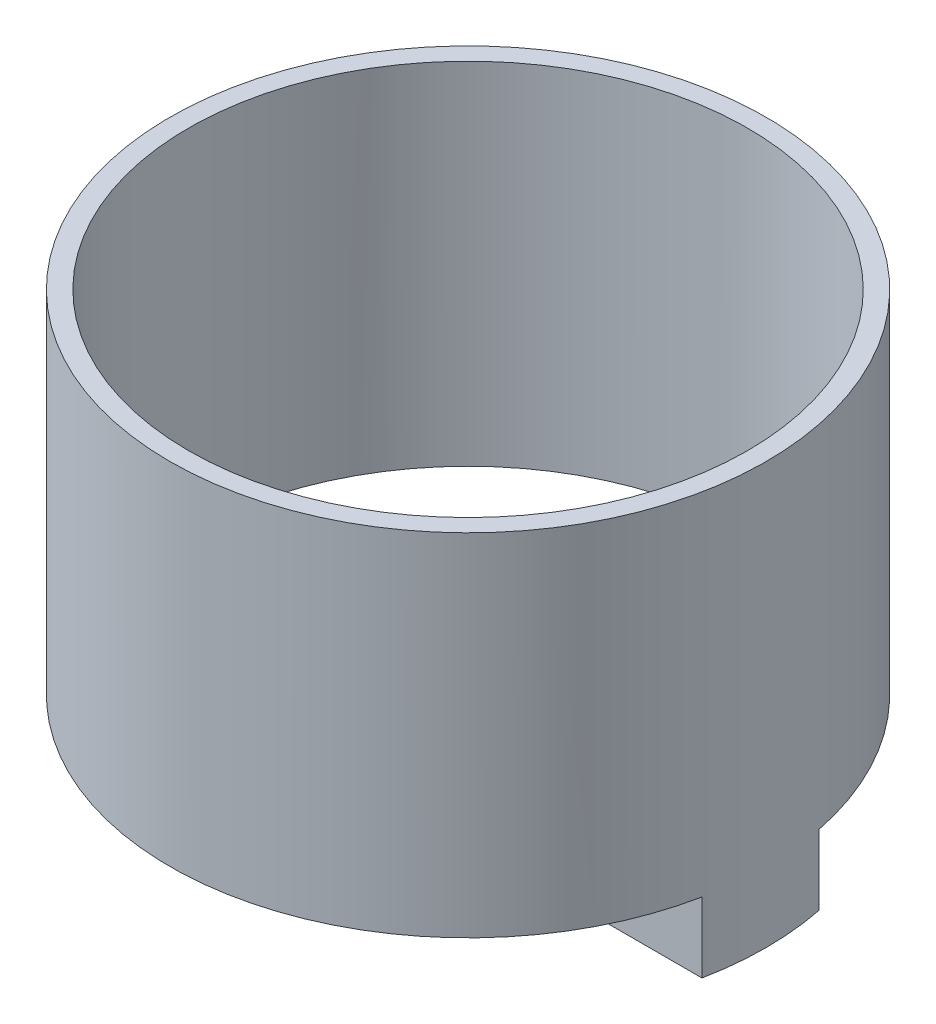
SolidWorks part; units mm, degrees
ref_plane "Front Plane" through (0, 0, 0) normal (0, 0, 1) x (1, 0, 0)
ref_plane "Top Plane" through (0, 0, 0) normal (0, 1, 0) x (1, 0, 0)
ref_plane "Right Plane" through (0, 0, 0) normal (1, 0, 0) x (0, 0, -1)
sketch "Sketch2" plane through (0, 0, 0) normal (0, 1, 0) x (1, 0, 0)
  circle A0 centre (0, 0) radius 11.95
  circle A1 centre (0, 0) radius 12.75
  dimension "D1" = 23.9
  dimension "D2" = 25.5
extrude "Boss-Extrude1" add sketch "Sketch2" along normal blind 15
sketch "Sketch3" plane through (0, 0, 0) normal (0, -1, 0) x (1, 0, 0)
  line L1 (5.25, -2.5) -> (5.25, 2.5)
  line L2 (5.25, 2.5) -> (12.5025, 2.5)
  line L3 (5.25, -2.5) -> (12.5025, -2.5)
  line L5 (-5.25, -2.5) -> (-12.5025, -2.5)
  line L6 (-5.25, -2.5) -> (-5.25, 2.5)
  line L7 (-5.25, 2.5) -> (-12.5025, 2.5)
  circle A0 centre (0, 0) radius 12.75 construction
  arc A1 (12.5025, 2.5) -> (12.5025, -2.5) centre (0, 0) cw
  arc A2 (-12.5025, 2.5) -> (-12.5025, -2.5) centre (0, 0) ccw
extrude "Boss-Extrude2" add sketch "Sketch3" along normal blind 3
